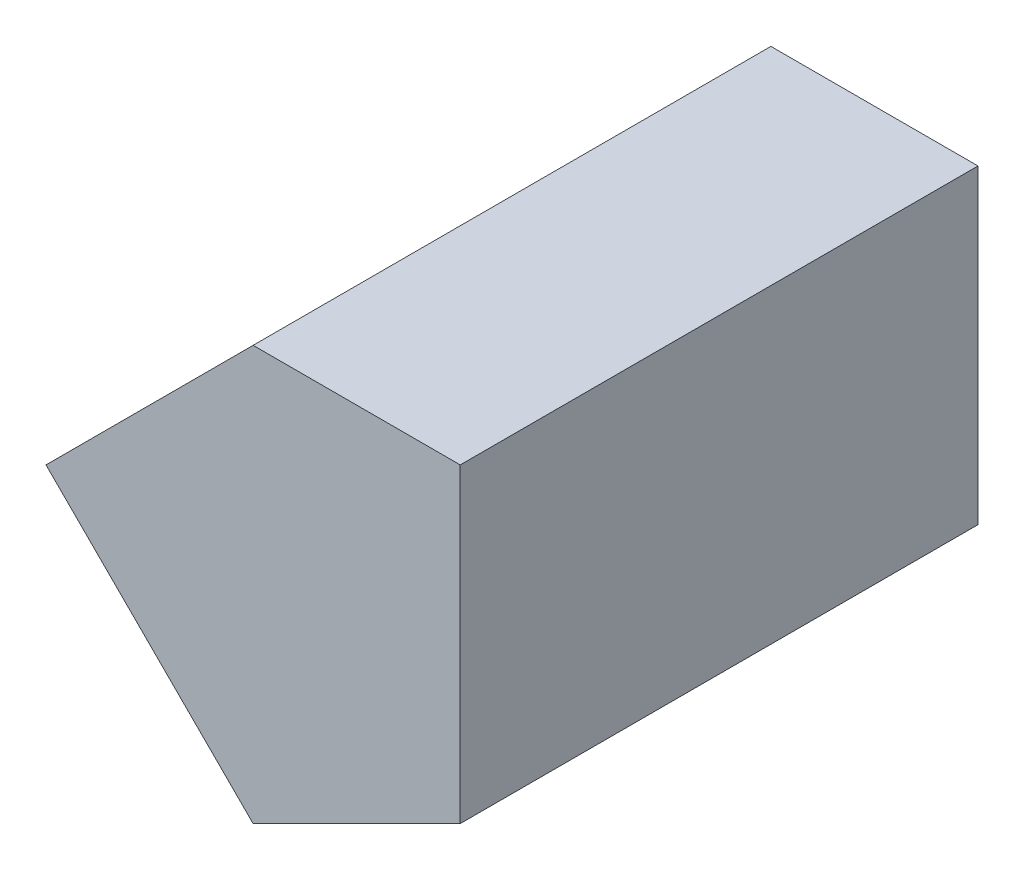
SolidWorks part; units mm, degrees
ref_plane "Front Plane" through (0, 0, 0) normal (0, 0, 1) x (1, 0, 0)
ref_plane "Top Plane" through (0, 0, 0) normal (0, 1, 0) x (1, 0, 0)
ref_plane "Right Plane" through (0, 0, 0) normal (1, 0, 0) x (0, 0, -1)
sketch "Sketch1" plane through (0, 0, 0) normal (0, 0, 1) x (1, 0, 0)
  line L0 (-20, 5) -> (-10, 15)
  line L1 (-10, 15) -> (0, 15)
  line L2 (0, 15) -> (0, 0)
  line L3 (0, 0) -> (-10, -5)
  line L4 (-10, -5) -> (-20, 5)
  dimension "D1" = 10
  dimension "D2" = 15
  dimension "D3" = 10
  dimension "D4" = 5
  dimension "D5" = 10
  dimension "D6" = 10
extrude "Boss-Extrude1" add sketch "Sketch1" along normal blind 25
